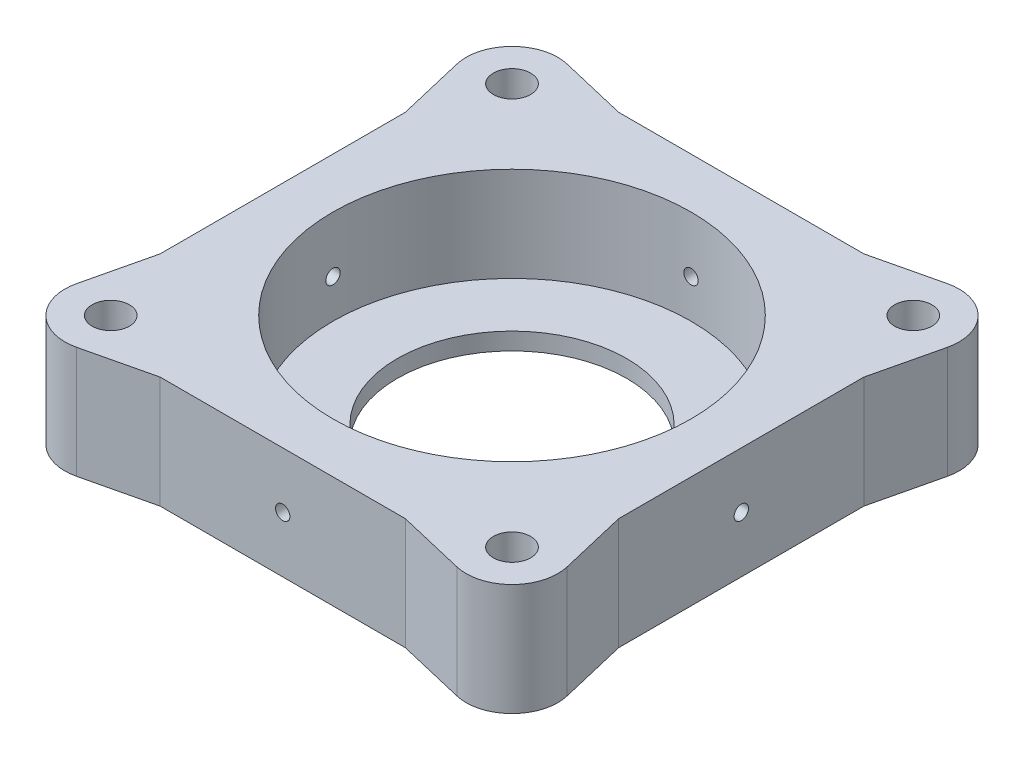
SolidWorks part; units mm, degrees
ref_plane "Front Plane" through (0, 0, 0) normal (0, 0, 1) x (1, 0, 0)
ref_plane "Top Plane" through (0, 0, 0) normal (0, 1, 0) x (1, 0, 0)
ref_plane "Right Plane" through (0, 0, 0) normal (1, 0, 0) x (0, 0, -1)
sketch "Sketch1" plane through (0, 0, 0) normal (0, 1, 0) x (1, 0, 0)
  line L0 (0, 35) -> (0, -35) construction
  line L1 (35, -35) -> (-35, -35)
  line L2 (35, -35) -> (35, 35)
  line L3 (35, 35) -> (-35, 35)
  line L4 (-35, -35) -> (-35, 35)
  line L5 (35, -35) -> (-35, 35) construction
  line L6 (35, 35) -> (-35, -35) construction
  line L7 (-35, 0) -> (35, 0) construction
  line L8 (-33.1578, 42.785) -> (7.8292, 33.0863)
  line L9 (-42.785, 33.1578) -> (-33.0863, -7.8292)
  line L10 (42.785, 33.1578) -> (33.0863, -7.8292)
  line L11 (33.1578, 42.785) -> (-7.8292, 33.0863)
  line L12 (-42.785, -33.1578) -> (-33.0863, 7.8292)
  line L13 (-33.1578, -42.785) -> (7.8292, -33.0863)
  line L14 (33.1578, -42.785) -> (-7.8292, -33.0863)
  line L15 (42.785, -33.1578) -> (33.0863, 7.8292)
  line L17 (40, -40) -> (-40, -40)
  line L18 (40, -40) -> (40, 40)
  line L19 (40, 40) -> (-40, 40)
  line L20 (-40, -40) -> (-40, 40)
  line L21 (40, -40) -> (-40, 40) construction
  line L22 (40, 40) -> (-40, -40) construction
  circle A0 centre (0, 0) radius 20
  circle A1 centre (0, 0) radius 34
  circle A2 centre (-35, 35) radius 3.25
  circle A3 centre (0, 0) radius 40
  circle A4 centre (-35, 35) radius 8
  circle A5 centre (35, 35) radius 3.25
  circle A6 centre (35, 35) radius 8
  circle A7 centre (-35, -35) radius 3.25
  circle A8 centre (-35, -35) radius 8
  circle A9 centre (35, -35) radius 3.25
  circle A10 centre (35, -35) radius 8
  dimension "D1" = 40
  dimension "D2" = 68
  dimension "D3" = 6.5
  dimension "D5" = 80
  dimension "D4" = 16
  dimension "D6" = 70
extrude "Boss-Extrude1" add sketch "Sketch1" along normal blind 19.5 contours L19 A4 L20 | L3 A4 L19 L20 L4 A2 | L4 A4 L3 A2 | A4 L9 L20 | A4 L20 L9 A3 L4 | A3 L9 L20 | L4 A3 L9 | L9 A3 L12 L4 | A3 L20 L12 | L12 A3 L4 | L20 A8 L4 A3 L12 | L12 A8 L20 | A8 L17 L20 | A8 L20 L17 L1 A7 L4 | A8 L4 A7 L1 | L4 A8 L1 A3 | L4 A3 L1 L13 L14 A1 L9 L12 | L3 A3 L4 L9 L12 A1 L11 L8 | A1 L12 L9 | A4 L4 A3 L3 | A4 L3 A3 L8 L19 | A4 L19 L8 | A3 L19 L8 | L8 A3 L3 | L11 A3 L8 L3 | A1 L8 L11 | L3 A3 L11 | L2 A3 L3 L11 L8 A1 L15 L10 | L3 A6 L19 L11 A3 | A3 L11 L19 | L19 A6 L11 | L2 A6 L3 A3 | A6 L2 A5 L3 | A6 L3 A5 L2 L18 L19 | A6 L19 L18 | L10 A6 L18 | L18 A6 L2 A3 L10 | A3 L18 L10 | L10 A3 L2 | L15 A3 L10 L2 | A3 L15 L18 | L2 A3 L15 | A1 L10 L15 | L1 A3 L2 L15 L10 A1 L13 L14 | A10 L18 L15 A3 L2 | A10 L15 L18 | A10 L2 A3 L1 | L18 A10 L2 A9 L1 L17 | L2 A10 L1 A9 | A10 L18 L17 | A10 L17 L14 | A10 L1 A3 L14 L17 | L14 A3 L1 | A3 L17 L14 | A3 L14 L1 L13 | A1 L14 L13 | L1 A3 L13 | A3 L13 L17 | L1 A8 L17 L13 A3 | L17 A8 L13 | A1 A0 | L11 L3 L8 | L15 L2 L10 | L1 L14 L13 | L4 L12 L9
sketch "Sketch2" plane through (0, 19.5, 0) normal (0, 1, 0) x (1, 0, 0)
  circle A0 centre (0, 0) radius 31.25
  dimension "D1" = 62.5
extrude "Cut-Extrude1" cut sketch "Sketch2" against normal blind 16.5
sketch "Sketch3" plane through (0, 0, 0) normal (0, -1, 0) x (1, 0, 0)
  circle A0 centre (-35, 35) radius 5.25
  circle A1 centre (35, 35) radius 5.25
  circle A2 centre (35, -35) radius 5.25
  circle A3 centre (-35, -35) radius 5.25
  dimension "D1" = 10.5
extrude "Cut-Extrude2" cut sketch "Sketch3" against normal blind 10
sketch "Sketch4" plane through (0, 0, 40) normal (0, 0, 1) x (1, 0, 0)
  line L0 (0, 0) -> (0, 19.5) construction
  line L1 (21.3883, 0) -> (-21.3883, 0) construction
  line L2 (21.3883, 19.5) -> (-21.3883, 19.5) construction
  circle A0 centre (0, 9.75) radius 1.25
  dimension "D1" = 2.5
extrude "Cut-Extrude3" cut sketch "Sketch4" against normal up to surface (80 mm away) up to face at (0, 9.75, -40)
sketch "Sketch5" plane through (40, 0, 0) normal (1, 0, 0) x (0, 0, -1)
  line L0 (0, 0) -> (0, 19.5) construction
  line L1 (-21.3883, 19.5) -> (21.3883, 19.5) construction
  line L2 (-21.3883, 0) -> (21.3883, 0) construction
  circle A0 centre (0, 9.75) radius 1.25
  dimension "D1" = 2.5
extrude "Cut-Extrude4" cut sketch "Sketch5" against normal up to surface (80 mm away) up to face at (-40, 9.75, 0)
sketch "Sketch6" [suppressed] plane through (0, 19.5, 0) normal (0, 1, 0) x (1, 0, 0)
  line L12 (21.3883, -40) -> (33.1578, -42.785)
  line L13 (42.785, -33.1578) -> (40, -21.3883)
  line L14 (40, -21.3883) -> (40, 21.3883)
  line L15 (40, 21.3883) -> (42.785, 33.1578)
  line L16 (33.1578, 42.785) -> (21.3883, 40)
  line L17 (21.3883, 40) -> (-21.3883, 40)
  line L18 (-21.3883, 40) -> (-33.1578, 42.785)
  line L19 (-42.785, 33.1578) -> (-40, 21.3883)
  line L20 (-40, 21.3883) -> (-40, -21.3883)
  line L21 (-40, -21.3883) -> (-42.785, -33.1578)
  line L22 (-33.1578, -42.785) -> (-21.3883, -40)
  line L23 (-21.3883, -40) -> (21.3883, -40)
  line L24 (21.3883, -40) -> (33.1578, -42.785)
  line L25 (42.785, -33.1578) -> (40, -21.3883)
  line L26 (40, -21.3883) -> (40, 21.3883)
  line L27 (40, 21.3883) -> (42.785, 33.1578)
  line L28 (33.1578, 42.785) -> (21.3883, 40)
  line L29 (21.3883, 40) -> (-21.3883, 40)
  line L30 (-21.3883, 40) -> (-33.1578, 42.785)
  line L31 (-42.785, 33.1578) -> (-40, 21.3883)
  line L32 (-40, 21.3883) -> (-40, -21.3883)
  line L33 (-40, -21.3883) -> (-42.785, -33.1578)
  line L34 (-33.1578, -42.785) -> (-21.3883, -40)
  line L35 (-21.3883, -40) -> (21.3883, -40)
  circle A0 centre (0, 0) radius 31.25 construction
  circle A1 centre (35, 35) radius 3.25 construction
  circle A2 centre (-35, 35) radius 3.25 construction
  circle A3 centre (35, -35) radius 3.25 construction
  arc A4 (33.1578, -42.785) -> (42.785, -33.1578) centre (35, -35) ccw
  arc A5 (42.785, 33.1578) -> (33.1578, 42.785) centre (35, 35) ccw
  arc A6 (-33.1578, 42.785) -> (-42.785, 33.1578) centre (-35, 35) ccw
  arc A7 (-42.785, -33.1578) -> (-33.1578, -42.785) centre (-35, -35) ccw
  arc A8 (33.1578, -42.785) -> (42.785, -33.1578) centre (35, -35) ccw
  arc A9 (42.785, 33.1578) -> (33.1578, 42.785) centre (35, 35) ccw
  arc A10 (-33.1578, 42.785) -> (-42.785, 33.1578) centre (-35, 35) ccw
  arc A11 (-42.785, -33.1578) -> (-33.1578, -42.785) centre (-35, -35) ccw
  circle A12 centre (-35, -35) radius 3.25 construction
  circle A13 centre (0, 0) radius 31.25
  circle A14 centre (35, 35) radius 3.25
  circle A15 centre (-35, 35) radius 3.25
  circle A16 centre (35, -35) radius 3.25
  circle A17 centre (-35, -35) radius 3.25
  dimension "D1" = 0
extrude "Boss-Extrude4" [suppressed] add sketch "Sketch6" along normal blind 3.5
sketch "Sketch7" [suppressed] plane through (0, 0, 0) normal (0, -1, 0) x (1, 0, 0)
  line L0 (-35, 35) -> (-38.7123, 38.7123) construction
  line L1 (-29.1444, 33.431) -> (-30.7134, 39.2866)
  line L2 (-30.7134, 39.2866) -> (-36.569, 40.8556)
  line L3 (-36.569, 40.8556) -> (-40.8556, 36.569)
  line L4 (-40.8556, 36.569) -> (-39.2866, 30.7134)
  line L5 (-39.2866, 30.7134) -> (-33.431, 29.1444)
  line L6 (-33.431, 29.1444) -> (-29.1444, 33.431)
  line L7 (39.2866, 30.7134) -> (40.8556, 36.569)
  line L8 (40.8556, 36.569) -> (36.569, 40.8556)
  line L9 (36.569, 40.8556) -> (30.7134, 39.2866)
  line L10 (30.7134, 39.2866) -> (29.1444, 33.431)
  line L11 (29.1444, 33.431) -> (33.431, 29.1444)
  line L12 (33.431, 29.1444) -> (39.2866, 30.7134)
  line L13 (30.7134, -39.2866) -> (36.569, -40.8556)
  line L14 (36.569, -40.8556) -> (40.8556, -36.569)
  line L15 (40.8556, -36.569) -> (39.2866, -30.7134)
  line L16 (39.2866, -30.7134) -> (33.431, -29.1444)
  line L17 (33.431, -29.1444) -> (29.1444, -33.431)
  line L18 (29.1444, -33.431) -> (30.7134, -39.2866)
  line L19 (-39.2866, -30.7134) -> (-40.8556, -36.569)
  line L20 (-40.8556, -36.569) -> (-36.569, -40.8556)
  line L21 (-36.569, -40.8556) -> (-30.7134, -39.2866)
  line L22 (-30.7134, -39.2866) -> (-29.1444, -33.431)
  line L23 (-29.1444, -33.431) -> (-33.431, -29.1444)
  line L24 (-33.431, -29.1444) -> (-39.2866, -30.7134)
  line L25 (0, 40) -> (0, -40) construction
  line L26 (21.3883, 40) -> (-21.3883, 40) construction
  line L27 (21.3883, -40) -> (-21.3883, -40) construction
  circle A0 centre (-35, 35) radius 5.25 construction
  point P32 (0, 0)
  dimension "D1" = 10.5
  dimension "D2" = 4
extrude "Cut-Extrude5" [suppressed] cut sketch "Sketch7" against normal offset from surface (21.5 mm away) 1.5
